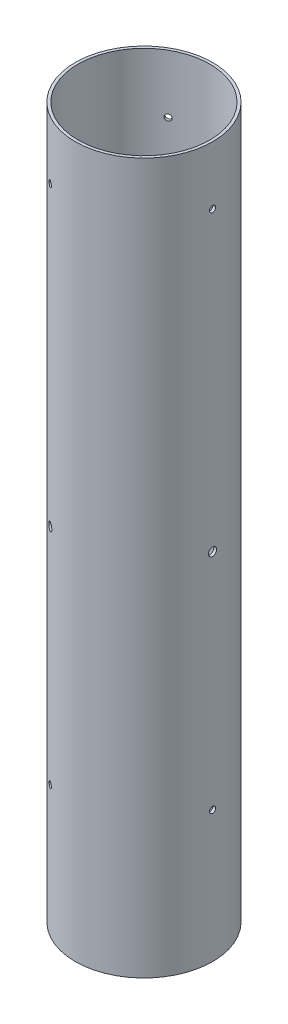
SolidWorks part; units mm, degrees
material "G10 Fiberglass"
ref_plane "Front Plane" through (0, 0, 0) normal (0, 0, 1) x (1, 0, 0)
ref_plane "Top Plane" through (0, 0, 0) normal (0, 1, 0) x (1, 0, 0)
ref_plane "Right Plane" through (0, 0, 0) normal (1, 0, 0) x (0, 0, -1)
sketch "Sketch1" plane through (0, 0, 0) normal (0, 1, 0) x (1, 0, 0)
  circle A0 centre (0, 0) radius 38.1635
  circle A1 centre (0, 0) radius 39.7891
  dimension "D1" = 76.327
  dimension "D2" = 1.6256
extrude "Boss-Extrude1" add sketch "Sketch1" along normal blind 411.48
ref_axis "Axis1" through (0, -7.62, 0) along (0, 1, 0)
ref_plane "Plane1" through (-19.8945, 0, 34.4584) normal (-0.5, 0, 0.866) x (0, -1, 0)
sketch "Sketch2" plane through (-19.8945, 0, 34.4584) normal (-0.5, 0, 0.866) x (0, -1, 0)
  line L0 (7.62, 0) -> (-160.02, 0) construction
  line L2 (0, -39.7891) -> (0, 39.7891) construction
  circle A0 centre (-76.2, 0) radius 1.778
  dimension "D1" = 76.2
  dimension "D2" = 3.556
extrude "Cut-Extrude1" cut sketch "Sketch2" against normal up to next
pattern_circular "CirPattern1" count 3 over 360 about axis through (0, -7.62, 0) along (0, 1, 0) of "Cut-Extrude1"
ref_plane "Plane2" through (0, 205.74, 0) normal (0, 1, 0) x (1, 0, 0)
sketch "Sketch3" plane through (-19.8945, 0, 34.4584) normal (-0.5, 0, 0.866) x (0, -1, 0)
  line L0 (-205.74, 43.768) -> (-205.74, -43.768) construction
  circle A0 centre (-205.74, 0) radius 2.3813
  dimension "D1" = 4.7625
extrude "Pressure Equalization Hole" cut sketch "Sketch3" against normal up to next
pattern_circular "CirPattern2" count 3 over 360 about axis through (0, -7.62, 0) along (0, 1, 0) of "Pressure Equalization Hole"
ref_plane "Plane3" through (39.7891, 0, 0) normal (1, 0, 0) x (0, 0, -1)
sketch "Sketch4" plane through (39.7891, 0, 0) normal (-1, 0, 0) x (0, -1, 0)
  line L0 (-411.48, 39.7891) -> (-411.48, -39.7891) construction
  circle A0 centre (-377.6726, 0) radius 1.7859
  dimension "D1" = 3.5719
  dimension "D2" = 33.8074
extrude "Cut-Extrude3" cut sketch "Sketch4" along normal up to next
pattern_circular "CirPattern3" count 3 over 360 about axis through (0, -7.62, 0) along (0, 1, 0) of "Cut-Extrude3"
